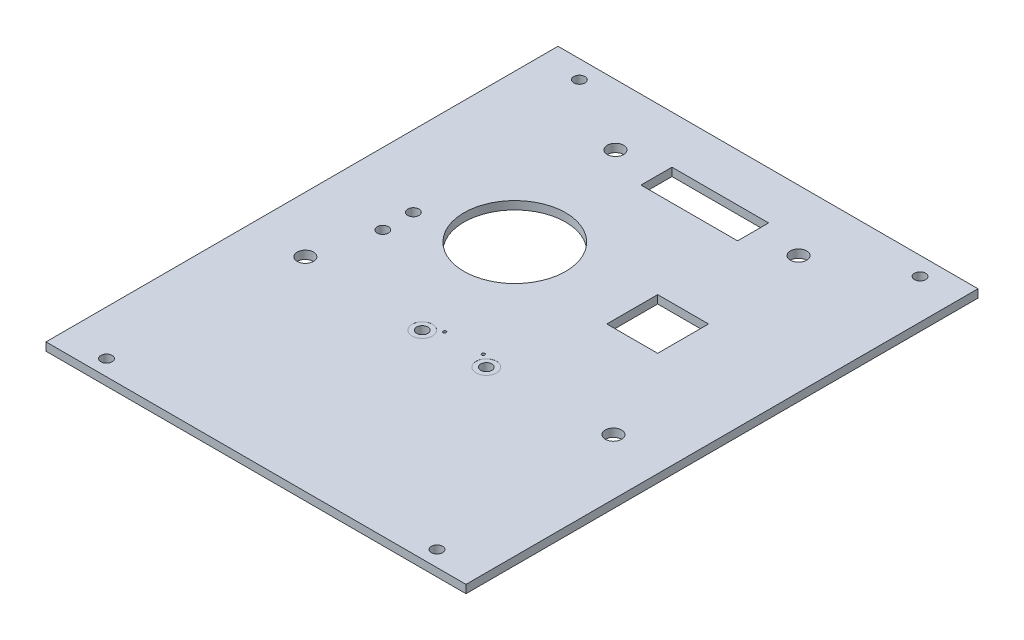
SolidWorks part; units mm, degrees
material "電力回路基板"
ref_plane "Front Plane" through (0, 0, 0) normal (0, 0, 1) x (1, 0, 0)
ref_plane "Top Plane" through (0, 0, 0) normal (0, 1, 0) x (1, 0, 0)
ref_plane "Right Plane" through (0, 0, 0) normal (1, 0, 0) x (0, 0, -1)
sketch "Sketch1" plane through (0, 0, 0) normal (0, 1, 0) x (1, 0, 0)
  line L0 (65.24, 0.2725) -> (65.24, -46.4375)
  line L1 (-17.76, 29.8625) -> (65.24, 29.8625)
  line L2 (65.24, 29.8625) -> (65.24, 21.5625)
  line L3 (-17.76, 4.3625) -> (-17.76, -45.7898)
  line L6 (65.24, -63.6375) -> (65.24, -70.1375)
  line L7 (65.24, -70.1375) -> (-17.76, -70.1375)
  line L8 (-17.76, -70.1375) -> (-17.76, -63.6375)
  line L11 (-17.76, 29.8625) -> (-17.76, 21.5625)
  line L17 (-17.76, -48.6375) -> (-17.76, -45.7898)
  line L21 (65.24, 6.5625) -> (65.24, 0.2725)
  line L22 (-17.76, 21.5625) -> (-17.76, 4.3625)
  line L23 (-17.76, -48.6375) -> (-17.76, -63.6375)
  line L24 (65.24, -46.4375) -> (65.24, -63.6375)
  line L25 (65.24, 6.5625) -> (65.24, 21.5625)
  circle A0 centre (20.04, -29.2375) radius 0.3
  circle A1 centre (27.74, -29.2375) radius 0.3
  dimension "D3" = 0.6
  dimension "D7" = 37.8
  dimension "D8" = 40.9
  dimension "D9" = 37.5
  dimension "D10" = 40.9
  dimension "D1" = 100
  dimension "D2" = 83
  dimension "D4" = 6.5
  dimension "D5" = 6.5
  dimension "D6" = 8.3
extrude "Boss-Extrude1" add sketch "Sketch1" along normal blind 1.6 contours L11 L22 L3 L17 L23 L8 L7 L6 L24 L0 L21 L25 L2 L1
hole_wizard "Ø2.2 (2.2) Diameter Hole1" positions "Sketch6" profile "Sketch5" hole size "Ø2.2" standard "ANSI Metric"
sketch "Sketch6" plane through (0, 1.6, 0) normal (0, 1, 0) x (1, 0, 0)
  line L2 (-17.76, 29.8625) -> (65.24, 29.8625) construction
  line L3 (-17.76, 29.8625) -> (-17.76, -70.1375) construction
  line L4 (65.24, 29.8625) -> (65.24, -70.1375) construction
  point P27 (57.24, 27.8625)
  point P29 (-9.76, 27.8625)
  dimension "D3" = 2
  dimension "D4" = 8
  dimension "D5" = 2
  dimension "D6" = 8
sketch "Sketch5" plane through (57.24, 1.6, -27.8625) normal (1, 0, 0) x (0, 0, 1)
  line L0 (0, 0) -> (0, 5)
  line L1 (0, 5) -> (1.1, 5)
  line L2 (1.1, 5) -> (1.1, 0)
  line L5 (1.1, 0) -> (0, 0)
  line L10 (0, 5) -> (-1.1, 5) construction
  line L11 (0, -6.35) -> (0, 107.95) construction
  dimension "Hole Dia." = 2.2
  dimension "Hole Depth" = 5
  dimension "Drill Angle" = 180
sketch "Sketch9" plane through (0, 0, 0) normal (0, -1, 0) x (-1, 0, 0)
  line L1 (17.76, 29.8625) -> (17.76, -70.1375) construction
  line L2 (17.76, 29.8625) -> (-65.24, 29.8625) construction
  circle A0 centre (-11.54, -6.1375) radius 10
  dimension "D1" = 29.3
  dimension "D3" = 36
  dimension "D4" = 20
extrude "Cut-Extrude4" cut sketch "Sketch9" against normal through all
sketch "Sketch15" plane through (0, 0, 0) normal (0, -1, 0) x (1, 0, 0)
  line L0 (-17.76, -29.8625) -> (-17.76, 70.1375) construction
  line L1 (65.24, 70.1375) -> (-17.76, 70.1375)
  line L2 (65.24, 70.1375) -> (65.24, 67.6375)
  line L3 (65.24, 67.6375) -> (-17.76, 67.6375)
  line L4 (-17.76, 70.1375) -> (-17.76, 67.6375)
  dimension "D1" = 2.5
extrude "Cut-Extrude8" cut sketch "Sketch15" against normal through all
sketch "Sketch16" plane through (0, 0, 0) normal (0, -1, 0) x (1, 0, 0)
  line L3 (-17.76, -29.8625) -> (65.24, -29.8625) construction
  line L5 (65.24, -29.8625) -> (65.24, 67.6375) construction
  line L6 (-17.76, -29.8625) -> (-17.76, 67.6375) construction
  line L7 (-17.76, 67.6375) -> (65.24, 67.6375) construction
  circle A0 centre (5.24, 56.6375) radius 1.5
  circle A1 centre (42.24, 56.6375) radius 1.5
  circle A5 centre (-13.76, 5.6375) radius 1.5
  circle A6 centre (61.24, 5.6375) radius 1.5
  circle A7 centre (2.24, 5.6375) radius 1.5
  point P2 (42.24, 56.6375)
  point P3 (5.24, 56.6375)
  point P23 (61.24, 5.6375)
  point P24 (-13.76, 5.6375)
  dimension "D10" = 3
  dimension "D11" = 3
  dimension "D19" = 3
  dimension "D20" = 3
  dimension "D21" = 3
  dimension "D22" = 20
  dimension "D23" = 62
  dimension "D5" = 11
  dimension "D6" = 23
  dimension "D7" = 11
  dimension "D8" = 23
  dimension "D15" = 35.5
  dimension "D16" = 35.5
  dimension "D17" = 4
  dimension "D18" = 4
sketch "Sketch37" plane through (0, 0, -29.8625) normal (0, 0, -1) x (-1, 0, 0)
  line L1 (17.76, 1.6) -> (-65.24, 1.6)
  line L2 (17.76, 1.6) -> (17.76, 0)
  line L3 (17.76, 0) -> (-65.24, 0)
  line L4 (-65.24, 1.6) -> (-65.24, 0)
extrude "Extrude1" add sketch "Sketch37" along normal blind 1.6
sketch "Sketch38" plane through (0, 0, 67.6375) normal (0, 0, 1) x (1, 0, 0)
  line L1 (65.24, 1.6) -> (-17.76, 1.6)
  line L2 (65.24, 1.6) -> (65.24, 0)
  line L3 (65.24, 0) -> (-17.76, 0)
  line L4 (-17.76, 1.6) -> (-17.76, 0)
extrude "Extrude2" add sketch "Sketch38" along normal blind 1.6
sketch "Sketch39" plane through (0, 1.6, 0) normal (0, 1, 0) x (1, 0, 0)
  line L0 (-17.76, -69.2375) -> (-17.76, 31.4625) construction
  line L1 (65.24, 31.4625) -> (65.24, -69.2375) construction
  line L2 (65.24, -69.2375) -> (-17.76, -69.2375) construction
  point P0 (-8.76, -66.1375)
  point P1 (56.24, -66.1375)
  dimension "D1" = 9
  dimension "D2" = 9
  dimension "D3" = 3.1
  dimension "D4" = 3.1
hole_wizard "Ø2.2 (2.2) Diameter Hole4" positions "Sketch41" profile "Sketch40" hole size "Ø2.2" standard "ANSI Metric"
sketch "Sketch41" plane through (0, 1.6, 0) normal (0, 1, 0) x (1, 0, 0)
  point P0 (-8.76, -66.1375)
  point P3 (56.24, -66.1375)
sketch "Sketch40" plane through (-8.76, 1.6, 66.1375) normal (1, 0, 0) x (0, 0, 1)
  line L0 (0, 0) -> (0, 1.6)
  line L1 (0, 1.6) -> (1.1, 1.6)
  line L2 (1.1, 1.6) -> (1.1, 0)
  line L5 (1.1, 0) -> (0, 0)
  line L10 (0, 1.6) -> (-1.1, 1.6) construction
  line L11 (0, -6.35) -> (0, 107.95) construction
  dimension "穴の直径" = 2.2
  dimension "穴の深さ" = 1.6
  dimension "ﾄﾞﾘﾙ角度" = 180
sketch "Sketch44" plane through (0, 0, 0) normal (0, -1, 0) x (1, 0, 0)
  line L0 (-17.76, 69.2375) -> (65.24, 69.2375) construction
  line L1 (65.24, -31.4625) -> (65.24, 69.2375) construction
  line L2 (-17.76, -31.4625) -> (-17.76, 69.2375) construction
  point P0 (43.24, 39.2375)
  point P1 (43.24, 22.2375)
  point P2 (4.24, 22.2375)
  point P3 (4.24, 39.2375)
  dimension "D1" = 30
  dimension "D2" = 22
  dimension "D3" = 22
  dimension "D4" = 17
  dimension "D5" = 17
  dimension "D6" = 30
  dimension "D7" = 22
  dimension "D8" = 22
sketch "Sketch49" plane through (0, 0, 0) normal (0, -1, 0) x (1, 0, 0)
  line L0 (-17.76, 69.2375) -> (65.24, 69.2375) construction
  line L1 (65.24, -31.4625) -> (65.04, -31.4625)
  line L2 (65.24, -31.4625) -> (65.24, 69.2375)
  line L3 (65.24, 69.2375) -> (65.04, 69.2375)
  line L4 (65.04, -31.4625) -> (65.04, 69.2375)
  line L5 (65.24, -31.4625) -> (-17.76, -31.4625) construction
  line L6 (-17.76, 69.2375) -> (-17.56, 69.2375)
  line L7 (-17.76, 69.2375) -> (-17.76, -31.4625)
  line L8 (-17.76, -31.4625) -> (-17.56, -31.4625)
  line L9 (-17.56, 69.2375) -> (-17.56, -31.4625)
  dimension "D1" = 0.2
  dimension "D2" = 0.2
extrude "Extrude5" cut sketch "Sketch49" against normal through all
sketch "Sketch51" plane through (0, 0, 0) normal (0, -1, 0) x (1, 0, 0)
  line L0 (65.04, -31.4625) -> (-17.56, -31.4625) construction
  line L1 (44.54, 1.0375) -> (34.54, 1.0375)
  line L2 (44.54, 1.0375) -> (44.54, 11.0375)
  line L3 (44.54, 11.0375) -> (34.54, 11.0375)
  line L4 (34.54, 1.0375) -> (34.54, 11.0375)
  line L5 (44.54, 1.0375) -> (34.54, 11.0375) construction
  line L6 (44.54, 11.0375) -> (34.54, 1.0375) construction
  line L8 (65.04, 69.2375) -> (65.04, -31.4625) construction
  point P0 (39.54, 6.0375)
  dimension "D1" = 37.5
  dimension "D2" = 25.5
extrude "Cut-Extrude9" cut sketch "Sketch51" against normal blind 10
sketch "Sketch52" plane through (0, 0, 0) normal (0, -1, 0) x (1, 0, 0)
  line L0 (65.04, -31.4625) -> (-17.56, -31.4625) construction
  line L1 (33.24, -15.9775) -> (14.24, -15.9775)
  line L2 (33.24, -15.9775) -> (33.24, -22.0775)
  line L3 (33.24, -22.0775) -> (14.24, -22.0775)
  line L4 (14.24, -15.9775) -> (14.24, -22.0775)
  line L5 (33.24, -15.9775) -> (14.24, -22.0775) construction
  line L6 (33.24, -22.0775) -> (14.24, -15.9775) construction
  point P0 (23.74, -19.0275)
  point P5 (23.74, -31.4625)
  dimension "D1" = 0
  dimension "D2" = 12.435
extrude "Cut-Extrude10" cut sketch "Sketch52" against normal through all
sketch "ｽｹｯﾁ1" plane through (0, 0, 0) normal (0, -1, 0) x (-1, 0, 0)
  line L0 (17.56, -69.2375) -> (-65.04, -69.2375) construction
  line L2 (17.56, 31.4625) -> (17.56, -69.2375) construction
  circle A2 centre (-14.44, -36.9875) radius 1.1
  circle A3 centre (-8.44, -36.9875) radius 1.1
  dimension "D5" = 32
  dimension "D6" = 32.25
  dimension "D7" = 32.25
  dimension "D8" = 26
sketch "ｽｹｯﾁ2" plane through (0, 0, 0) normal (0, -1, 0) x (-1, 0, 0)
  line L0 (17.56, -69.2375) -> (-65.04, -69.2375) construction
  line L1 (-65.04, -69.2375) -> (-65.04, 31.4625) construction
  line L2 (17.56, 31.4625) -> (17.56, -69.2375) construction
  line L3 (-65.04, 31.4625) -> (17.56, 31.4625) construction
  circle A0 centre (-54.04, -29.2375) radius 1.6
  circle A1 centre (6.56, -29.2375) radius 1.6
  circle A2 centre (-41.74, 19.4625) radius 1.6
  circle A3 centre (-5.74, 19.4625) radius 1.6
  dimension "D1" = 40
  dimension "D2" = 11
  dimension "D3" = 11
  dimension "D4" = 40
  dimension "D5" = 23.3
  dimension "D6" = 23.3
  dimension "D7" = 12
  dimension "D8" = 12
extrude "ｶｯﾄ - 押し出し2" cut sketch "ｽｹｯﾁ2" against normal blind 10
sketch "ｽｹｯﾁ8" plane through (0, 1.6, 0) normal (0, 1, 0) x (1, 0, 0)
  line L0 (65.04, -69.2375) -> (-17.56, -69.2375) construction
  circle A0 centre (27.54, -28.3375) radius 0.3
  circle A1 centre (19.94, -28.3375) radius 0.3
  dimension "D1" = 40.9
  dimension "D2" = 40.9
extrude "ｶｯﾄ - 押し出し3" cut sketch "ｽｹｯﾁ8" against normal blind 10
sketch "ｽｹｯﾁ9" plane through (0, 1.6, 0) normal (0, 1, 0) x (1, 0, 0)
  line L0 (65.04, -69.2375) -> (-17.56, -69.2375) construction
  line L1 (-17.56, 31.4625) -> (-17.56, -69.2375) construction
  line L2 (65.04, -69.2375) -> (65.04, 31.4625) construction
  circle A0 centre (30.04, -30.2375) radius 1.1
  circle A1 centre (17.44, -30.2375) radius 1.1
  dimension "D1" = 39
  dimension "D2" = 39
  dimension "D3" = 35
  dimension "D4" = 35
extrude "ｶｯﾄ - 押し出し4" cut sketch "ｽｹｯﾁ9" against normal blind 10
sketch "ｽｹｯﾁ10" plane through (0, 1.6, 0) normal (0, 1, 0) x (1, 0, 0)
  circle A0 centre (30.04, -30.2375) radius 2
  circle A1 centre (17.44, -30.2375) radius 2
extrude "ｶｯﾄ - 押し出し5" cut sketch "ｽｹｯﾁ10" against normal blind 0.01
ref_point "点2"
ref_point "点3"
ref_point "点4"
ref_point "点5"
ref_point "点6"
ref_point "点7"
ref_point "点8"
ref_point "点9"
ref_point "点10"
sketch "ｽｹｯﾁ11" plane through (0, 1.6, 0) normal (0, 1, 0) x (1, 0, 0)
  line L1 (-17.56, 31.4625) -> (65.04, 31.4625) construction
  line L2 (-17.56, 31.4625) -> (-17.56, -69.2375) construction
  circle A0 centre (-3.51, -11.0375) radius 1.1
  circle A1 centre (-3.51, -17.0375) radius 1.1
  dimension "D1" = 14.05
  dimension "D3" = 2.2
  dimension "D4" = 2.2
  dimension "D5" = 42.5
  dimension "D6" = 6
extrude "ｶｯﾄ - 押し出し6" cut sketch "ｽｹｯﾁ11" against normal blind 10
